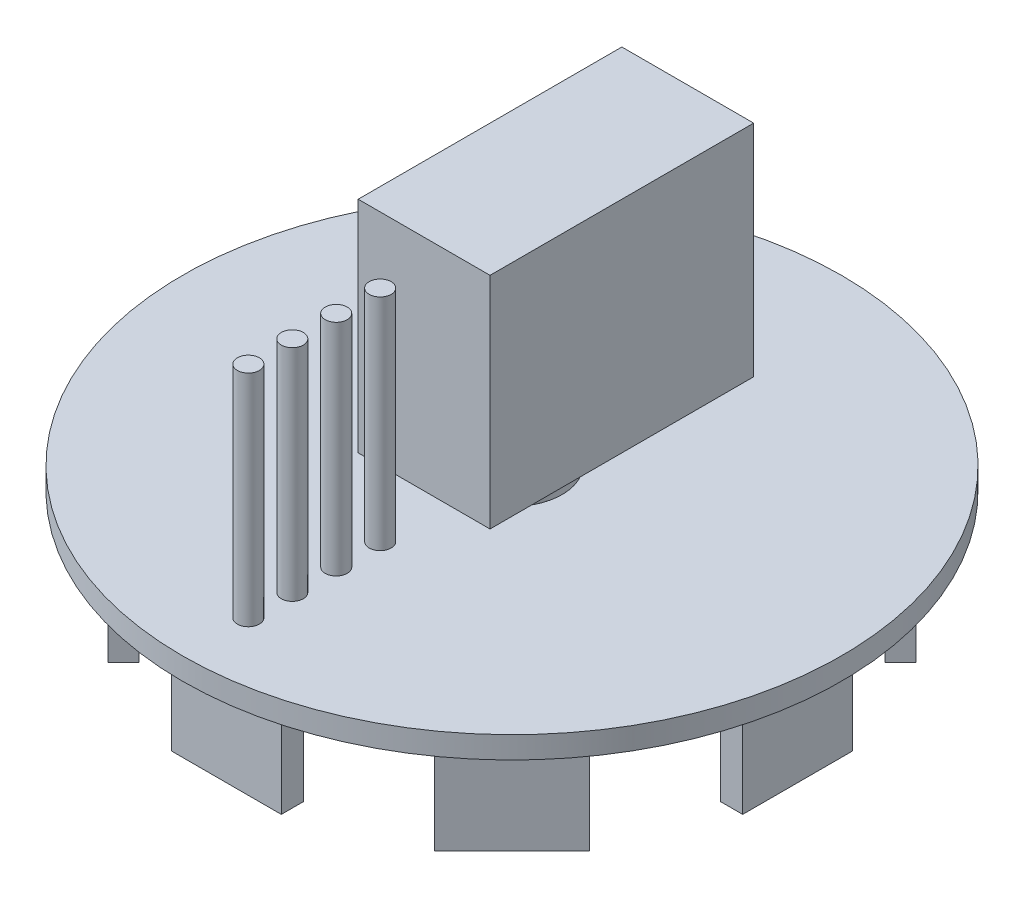
SolidWorks part; units mm, degrees
ref_plane "Front Plane" through (0, 0, 0) normal (0, 0, 1) x (1, 0, 0)
ref_plane "Top Plane" through (0, 0, 0) normal (0, 1, 0) x (1, 0, 0)
ref_plane "Right Plane" through (0, 0, 0) normal (1, 0, 0) x (0, 0, -1)
sketch "Sketch1" plane through (0, 0, 0) normal (0, 1, 0) x (1, 0, 0)
  line L0 (37.1231, 54.8008) -> (33.5876, 51.2652)
  line L1 (-12.5, 65) -> (12.5, 65)
  line L2 (-12.5, 65) -> (-12.5, 60)
  line L3 (-12.5, 60) -> (12.5, 60)
  line L4 (12.5, 65) -> (12.5, 60)
  line L5 (37.1231, 54.8008) -> (54.8008, 37.1231)
  line L6 (54.8008, 37.1231) -> (51.2652, 33.5876)
  line L7 (33.5876, 51.2652) -> (51.2652, 33.5876)
  line L8 (65, 12.5) -> (60, 12.5)
  line L9 (65, 12.5) -> (65, -12.5)
  line L10 (65, -12.5) -> (60, -12.5)
  line L11 (60, 12.5) -> (60, -12.5)
  line L12 (54.8008, -37.1231) -> (51.2652, -33.5876)
  line L13 (54.8008, -37.1231) -> (37.1231, -54.8008)
  line L14 (37.1231, -54.8008) -> (33.5876, -51.2652)
  line L15 (51.2652, -33.5876) -> (33.5876, -51.2652)
  line L16 (12.5, -65) -> (12.5, -60)
  line L17 (12.5, -65) -> (-12.5, -65)
  line L18 (-12.5, -65) -> (-12.5, -60)
  line L19 (12.5, -60) -> (-12.5, -60)
  line L20 (-37.1231, -54.8008) -> (-33.5876, -51.2652)
  line L21 (-37.1231, -54.8008) -> (-54.8008, -37.1231)
  line L22 (-54.8008, -37.1231) -> (-51.2652, -33.5876)
  line L23 (-33.5876, -51.2652) -> (-51.2652, -33.5876)
  line L24 (-65, -12.5) -> (-60, -12.5)
  line L25 (-65, -12.5) -> (-65, 12.5)
  line L26 (-65, 12.5) -> (-60, 12.5)
  line L27 (-60, -12.5) -> (-60, 12.5)
  line L28 (-54.8008, 37.1231) -> (-51.2652, 33.5876)
  line L29 (-54.8008, 37.1231) -> (-37.1231, 54.8008)
  line L30 (-37.1231, 54.8008) -> (-33.5876, 51.2652)
  line L31 (-51.2652, 33.5876) -> (-33.5876, 51.2652)
  circle A0 centre (0, 0) radius 75
  point P7 (0, 60)
  point P38 (0, 0)
  dimension "D1" = 150
  dimension "D2" = 25
  dimension "D3" = 5
  dimension "D4" = 65
  dimension "D5" = 8
extrude "Boss-Extrude1" add sketch "Sketch1" along normal blind 25 contours L20 L23 L22 L21 | L28 L31 L30 L29 | L4 L1 L2 L3 | L0 L7 L6 L5 | L8 L11 L10 L9 | L12 L15 L14 L13 | L16 L19 L18 L17 | L24 L27 L26 L25
sketch "Sketch2" plane through (0, 25, 0) normal (0, 1, 0) x (1, 0, 0)
  circle A0 centre (0, 0) radius 75
  dimension "D1" = 150
extrude "Boss-Extrude2" add sketch "Sketch2" along normal blind 5
sketch "Sketch3" plane through (0, 25, 0) normal (0, -1, 0) x (1, 0, 0)
  line L1 (-15, 50) -> (15, 50)
  line L2 (-15, 50) -> (-15, 20)
  line L3 (-15, 20) -> (15, 20)
  line L4 (15, 50) -> (15, 20)
  dimension "D1" = 30
  dimension "D2" = 30
  dimension "D3" = 20
  dimension "D4" = 15
extrude "Boss-Extrude3" add sketch "Sketch3" along normal blind 5
sketch "Sketch4" plane through (0, 25, 0) normal (0, -1, 0) x (1, 0, 0)
  circle A0 centre (0, 0) radius 11.4203
extrude "Cut-Extrude1" cut sketch "Sketch4" against normal blind 5
sketch "Sketch5" plane through (0, 30, 0) normal (0, 1, 0) x (1, 0, 0)
  circle A0 centre (0, 0) radius 11.4203
extrude "Boss-Extrude4" add sketch "Sketch5" along normal blind 5 separate body
sketch "Sketch6" plane through (0, 35, 0) normal (0, 1, 0) x (1, 0, 0)
  line L1 (-15, -20) -> (15, -20)
  line L2 (-15, -20) -> (-15, 40)
  line L3 (-15, 40) -> (15, 40)
  line L4 (15, -20) -> (15, 40)
  circle A0 centre (0, 0) radius 11.4203 construction
  dimension "D3" = 20
  dimension "D1" = 60
  dimension "D2" = 30
  dimension "D4" = 15
extrude "Boss-Extrude5" add sketch "Sketch6" along normal blind 50
sketch "Sketch7" plane through (0, 30, 0) normal (0, 1, 0) x (1, 0, 0)
  circle A0 centre (0, -30) radius 2.5
  circle A1 centre (0, -40) radius 2.5
  circle A2 centre (0, -50) radius 2.5
  circle A3 centre (0, -60) radius 2.5
  dimension "D1" = 5
  dimension "D2" = 5
  dimension "D3" = 5
  dimension "D4" = 5
  dimension "D5" = 30
  dimension "D6" = 10
  dimension "D7" = 10
  dimension "D8" = 10
extrude "Boss-Extrude6" add sketch "Sketch7" along normal blind 50
